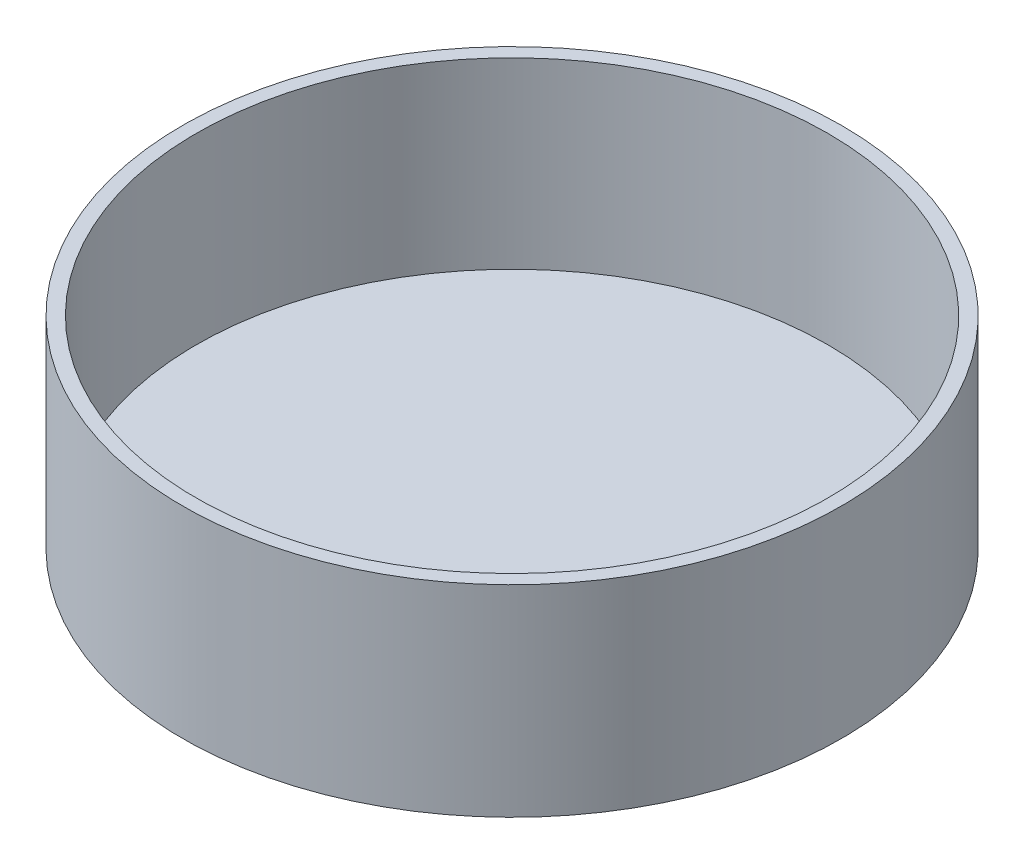
SolidWorks part; units mm, degrees
ref_plane "Front" through (0, 0, 0) normal (0, 0, 1) x (1, 0, 0)
ref_plane "Top" through (0, 0, 0) normal (0, 1, 0) x (1, 0, 0)
ref_plane "Right" through (0, 0, 0) normal (1, 0, 0) x (0, 0, -1)
sketch "Sketch1" plane through (0, 0, 0) normal (1, 0, 0) x (0, 0, -1)
  line L0 (0, 0) -> (-114.3, 0)
  line L1 (-114.3, 0) -> (-114.3, 69.85)
  line L2 (-114.3, 69.85) -> (-109.5375, 69.85)
  line L3 (-109.5375, 69.85) -> (-109.5375, 6.35)
  line L4 (-109.5375, 6.35) -> (0, 6.35)
  line L5 (0, 6.35) -> (0, 0)
  line L6 (0, -45.6337) -> (0, 123.0648) construction
  dimension "D1" = 219.075
  dimension "D2" = 4.7625
  dimension "D3" = 69.85
  dimension "D4" = 63.5
revolve "Revolve1" add sketch "Sketch1" angle 360 about L6
